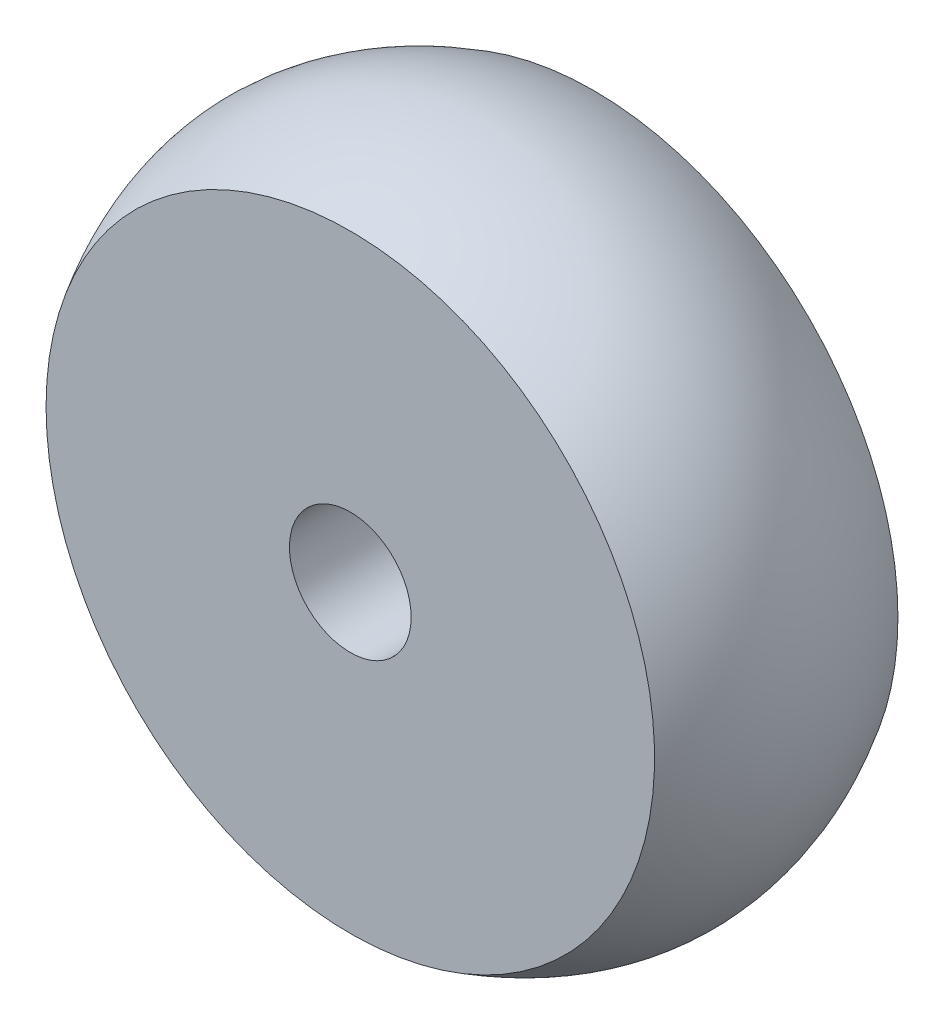
SolidWorks part; units mm, degrees
ref_plane "Front Plane" through (0, 0, 0) normal (0, 0, 1) x (1, 0, 0)
ref_plane "Top Plane" through (0, 0, 0) normal (0, 1, 0) x (1, 0, 0)
ref_plane "Right Plane" through (0, 0, 0) normal (1, 0, 0) x (0, 0, -1)
sketch "Sketch1" plane through (0, 0, 0) normal (0, 0, 1) x (1, 0, 0)
  circle A0 centre (0, 0) radius 12.5
  circle A1 centre (0, 0) radius 2.5
  dimension "D1" = 25
  dimension "D2" = 5
extrude "Boss-Extrude1" add sketch "Sketch1" along normal blind 10
sketch "Sketch2" plane through (0, 0, 0) normal (1, 0, 0) x (0, 0, -1)
  line L0 (0, 12.5) -> (-10, 12.5) construction
  line L1 (0, 0) -> (-16.0604, 0) construction
  line L2 (-10, 12.5) -> (0, 12.5)
  spline S0 degree 2 poles (-10, 12.5) (-5, 15.5) (0, 12.5) knots 0 0 0 1 1 1
  dimension "D1" = 1.5
revolve "Revolve1" add sketch "Sketch2" angle 360 about L1
